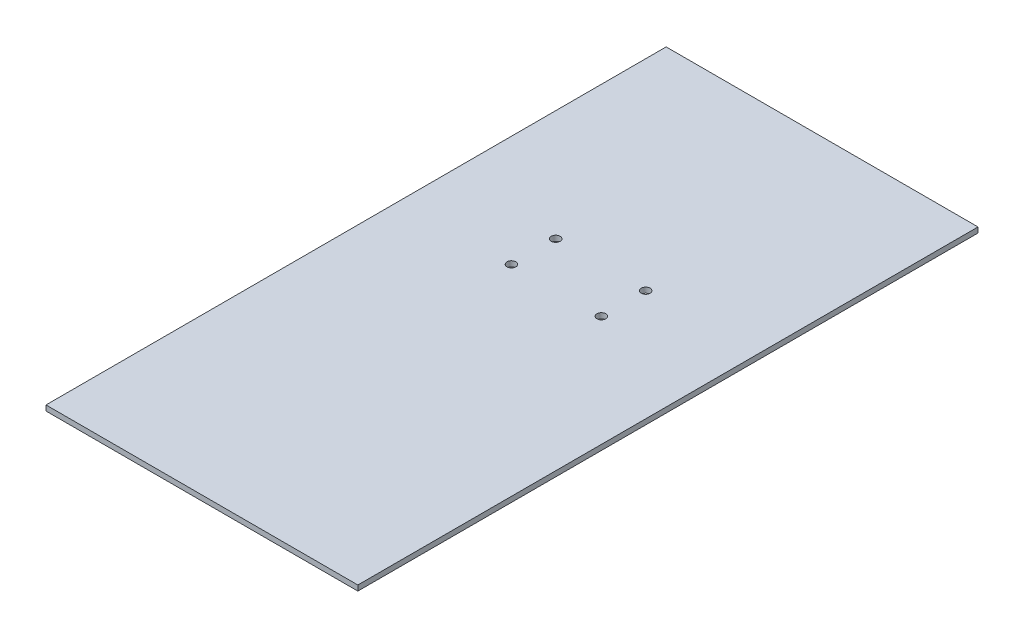
SolidWorks part; units mm, degrees
ref_plane "Front Plane" through (0, 0, 0) normal (0, 0, 1) x (1, 0, 0)
ref_plane "Top Plane" through (0, 0, 0) normal (0, 1, 0) x (1, 0, 0)
ref_plane "Right Plane" through (0, 0, 0) normal (1, 0, 0) x (0, 0, -1)
sketch "Sketch1" plane through (0, 0, 0) normal (0, 1, 0) x (1, 0, 0)
  line L1 (0, 0) -> (176, 0)
  line L2 (0, 0) -> (0, 350)
  line L3 (0, 350) -> (176, 350)
  line L4 (176, 0) -> (176, 350)
  dimension "D1" = 350
  dimension "D2" = 176
extrude "Boss-Extrude1" add sketch "Sketch1" along normal blind 3
hole_wizard "Ø5.0mm Dowel Hole1" positions "Sketch2" profile "Sketch3" hole size "Ø5.0" standard "ANSI Metric" end condition up to next
sketch "Sketch2" plane through (0, 0, 0) normal (0, -1, 0) x (-1, 0, 0)
  point P0 (-113.3996, 225.06)
  point P3 (-113.3996, 200.06)
  point P6 (-62.6247, 225.06)
  point P9 (-62.6247, 200.06)
sketch "Sketch3" plane through (113.3996, 0, -225.06) normal (1, 0, 0) x (0, 0, -1)
  line L0 (0, 0) -> (0, 3)
  line L1 (0, 3) -> (2.5, 3)
  line L2 (2.5, 3) -> (2.5, 0)
  line L5 (2.5, 0) -> (0, 0)
  line L11 (0, -6.35) -> (0, 107.95) construction
  dimension "Thru Hole Dia." = 5
  dimension "Thru Hole Depth" = 3
